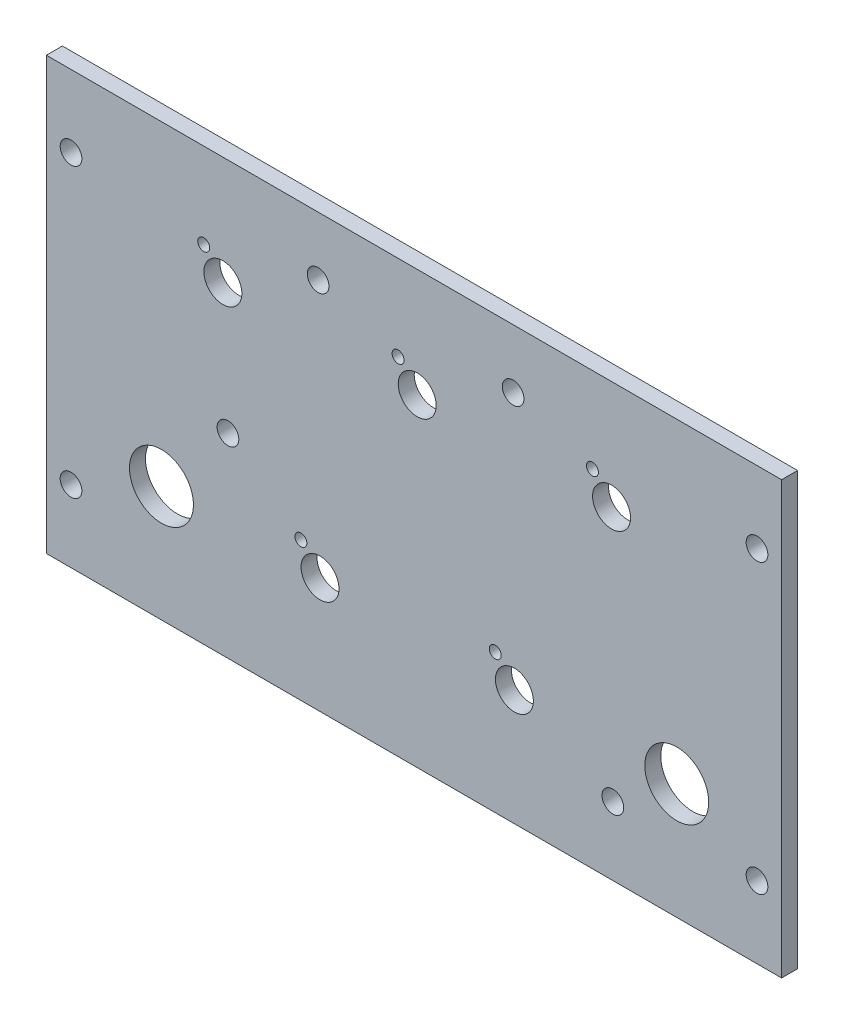
SolidWorks part; units mm, degrees
ref_plane "Front Plane" through (0, 0, 0) normal (0, 0, 1) x (1, 0, 0)
ref_plane "Top Plane" through (0, 0, 0) normal (0, 1, 0) x (1, 0, 0)
ref_plane "Right Plane" through (0, 0, 0) normal (1, 0, 0) x (0, 0, -1)
sketch "Sketch1" plane through (0, 0, 0) normal (0, 0, 1) x (1, 0, 0)
  line L4 (0, 85.725) -> (-146.05, 85.725)
  line L5 (-146.05, 85.725) -> (-146.05, 0)
  line L6 (-146.05, 0) -> (0, 0)
  line L7 (0, 0) -> (0, 85.725)
  line L8 (0, 85.725) -> (-146.05, 85.725)
  line L9 (-146.05, 85.725) -> (-146.05, 0)
  line L10 (-146.05, 0) -> (0, 0)
  line L11 (0, 0) -> (0, 85.725)
  dimension "D1" = 0
extrude "Boss-Extrude1" add sketch "Sketch1" against normal blind 3.175
hole_wizard "#6 Clearance Hole1" positions "Sketch3" profile "Sketch2" hole size "#6" standard "ANSI Inch"
sketch "Sketch3" plane through (0, 0, -3.175) normal (0, 0, -1) x (-1, 0, 0)
  point P0 (4.8895, 71.4375)
  point P3 (53.34, 74.041)
  point P6 (92.075, 74.041)
  point P9 (141.1605, 71.4375)
  point P12 (109.982, 38.735)
  point P15 (141.1605, 14.2875)
  point P18 (33.528, 13.589)
  point P21 (4.8895, 14.2875)
sketch "Sketch2" plane through (-4.8895, 71.4375, -3.175) normal (1, 0, 0) x (0, 1, 0)
  line L0 (0, 0) -> (0, 13.9934)
  line L1 (0, 13.9934) -> (2.1526, 12.7)
  line L2 (2.1526, 12.7) -> (2.1526, 0)
  line L5 (2.1526, 0) -> (0, 0)
  line L10 (0, 13.9934) -> (-2.1526, 12.7) construction
  line L11 (0, -6.35) -> (0, 107.95) construction
  dimension "Hole Dia." = 4.3053
  dimension "Hole Depth" = 12.7
  dimension "Drill Angle" = 118
sketch "Sketch4" plane through (0, 0, -3.175) normal (0, 0, -1) x (-1, 0, 0)
  circle A0 centre (20.828, 22.987) radius 6.35
  circle A1 centre (123.19, 22.987) radius 6.35
  circle A2 centre (33.782, 64.135) radius 3.7703
  circle A3 centre (72.39, 64.135) radius 3.7703
  circle A4 centre (110.998, 64.135) radius 3.7703
  circle A5 centre (91.694, 22.987) radius 3.7703
  circle A6 centre (53.086, 22.987) radius 3.7703
  circle A7 centre (37.5823, 68.778) radius 1.1906
  circle A8 centre (76.1903, 68.778) radius 1.1906
  circle A9 centre (114.7983, 68.778) radius 1.1906
  circle A10 centre (56.8863, 27.63) radius 1.1906
  circle A11 centre (95.4943, 27.63) radius 1.1906
  dimension "D1" = 12.7
  dimension "D2" = 7.5406
  dimension "D3" = 2.3813
extrude "Cut-Extrude1" cut sketch "Sketch4" against normal through all
